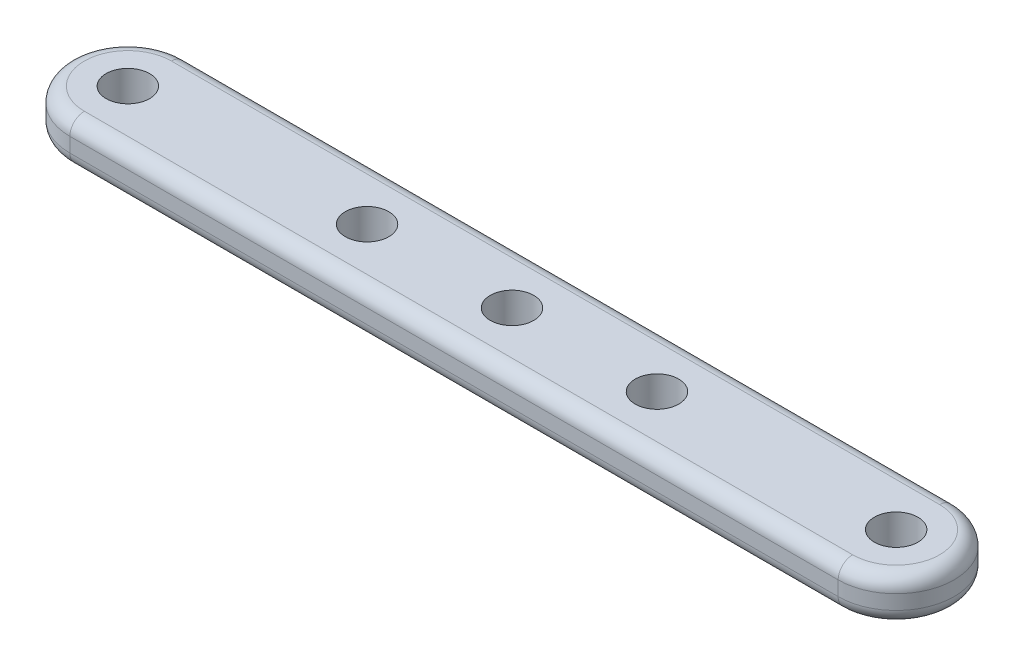
SolidWorks part; units mm, degrees
ref_plane "Front Plane" through (0, 0, 0) normal (0, 0, 1) x (1, 0, 0)
ref_plane "Top Plane" through (0, 0, 0) normal (0, 1, 0) x (1, 0, 0)
ref_plane "Right Plane" through (0, 0, 0) normal (1, 0, 0) x (0, 0, -1)
sketch "Sketch1" plane through (0, 0, 0) normal (0, 1, 0) x (1, 0, 0)
  line L0 (-26.5, 4) -> (26.5, 4)
  line L1 (-26.5, -4) -> (26.5, -4)
  line L2 (-2.75, 0) -> (2.75, 0) construction
  line L3 (0, -55) -> (0, 55) construction
  line L4 (-6, -4) -> (-6, -24)
  line L5 (-6, -24) -> (6, -24)
  line L6 (6, -24) -> (6, -4)
  line L13 (7.75, 4) -> (7.75, -4)
  line L14 (59.75, 4) -> (59.75, -4)
  arc A0 (-26.5, 4) -> (-26.5, -4) centre (-26.5, 0) ccw
  arc A1 (26.5, 4) -> (26.5, -4) centre (26.5, 0) cw
  circle A2 centre (-26.5, 0) radius 1.5
  circle A3 centre (26.5, 0) radius 1.5
  circle A4 centre (-10, 0) radius 1.5
  circle A5 centre (10, 0) radius 1.5
  circle A6 centre (0, 0) radius 1.5
  circle A7 centre (0, -20) radius 1.5
  dimension "D1" = 3
  dimension "D3" = 53
  dimension "D7" = 12
  dimension "D2" = 8
  dimension "D4" = 26.5
  dimension "D5" = 10
  dimension "D6" = 10
  dimension "D8" = 6
  dimension "D9" = 20
  dimension "D10" = 20
extrude "Boss-Extrude1" add sketch "Sketch1" along normal blind 3 contours L0 A0 L1 L13 A2 | L14 L0 L13 L1 A6 A5 A4 | A1 L0 L14 L1 A3
fillet "Fillet1" radius 1 8 edges at (30.5, 0, 0) (30.5, 3, 0) (-30.5, 0, 0) (-30.5, 3, 0) (0, 0, 4) (0, 3, 4) (0, 0, -4) (0, 3, -4)
